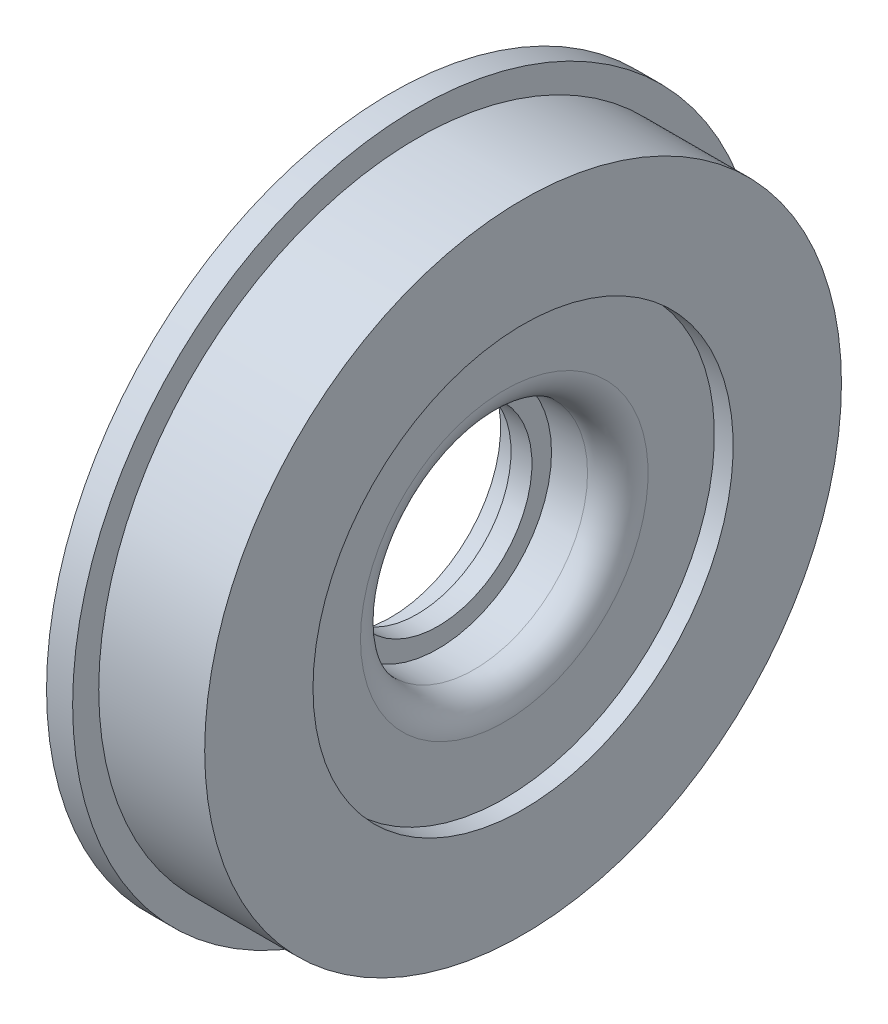
SolidWorks part; units mm, degrees
material "Perspex (TM) GS Acrylic Cast Sheet"
ref_plane "Front Plane" through (0, 0, 0) normal (0, 0, 1) x (1, 0, 0)
ref_plane "Top Plane" through (0, 0, 0) normal (0, 1, 0) x (1, 0, 0)
ref_plane "Right Plane" through (0, 0, 0) normal (1, 0, 0) x (0, 0, -1)
sketch "Sketch1" plane through (0, 0, 0) normal (0, 0, 1) x (1, 0, 0)
  line L0 (0, 0) -> (64.7955, 0) construction
  line L1 (0, 21) -> (5, 21)
  line L2 (5, 21) -> (5, 18)
  line L3 (5, 18) -> (9, 18)
  line L4 (9, 18) -> (9, 21.75)
  line L5 (9, 21.75) -> (15.9, 21.75)
  line L6 (21.7, 27.55) -> (21.7, 40.25)
  line L7 (21.7, 40.25) -> (25.3, 40.25)
  line L8 (25.3, 40.25) -> (25.3, 61)
  line L9 (25.3, 61) -> (5, 61)
  line L10 (5, 61) -> (5, 66)
  line L11 (5, 66) -> (0, 66)
  line L12 (0, 66) -> (0, 21)
  line L13 (0, 0) -> (0, 92.9456) construction
  arc A0 (15.9, 21.75) -> (21.7, 27.55) centre (15.9, 27.55) ccw
  point P5 (9, 19.875)
  dimension "D12" = 5.8
  dimension "D1" = 21
  dimension "D2" = 18
  dimension "D3" = 5
  dimension "D4" = 5
  dimension "D5" = 3.6
  dimension "D6" = 21.75
  dimension "D7" = 40.25
  dimension "D8" = 25.3
  dimension "D9" = 16.3
  dimension "D10" = 61
  dimension "D11" = 66
revolve "Body" add sketch "Sketch1" angle 360 about L0
